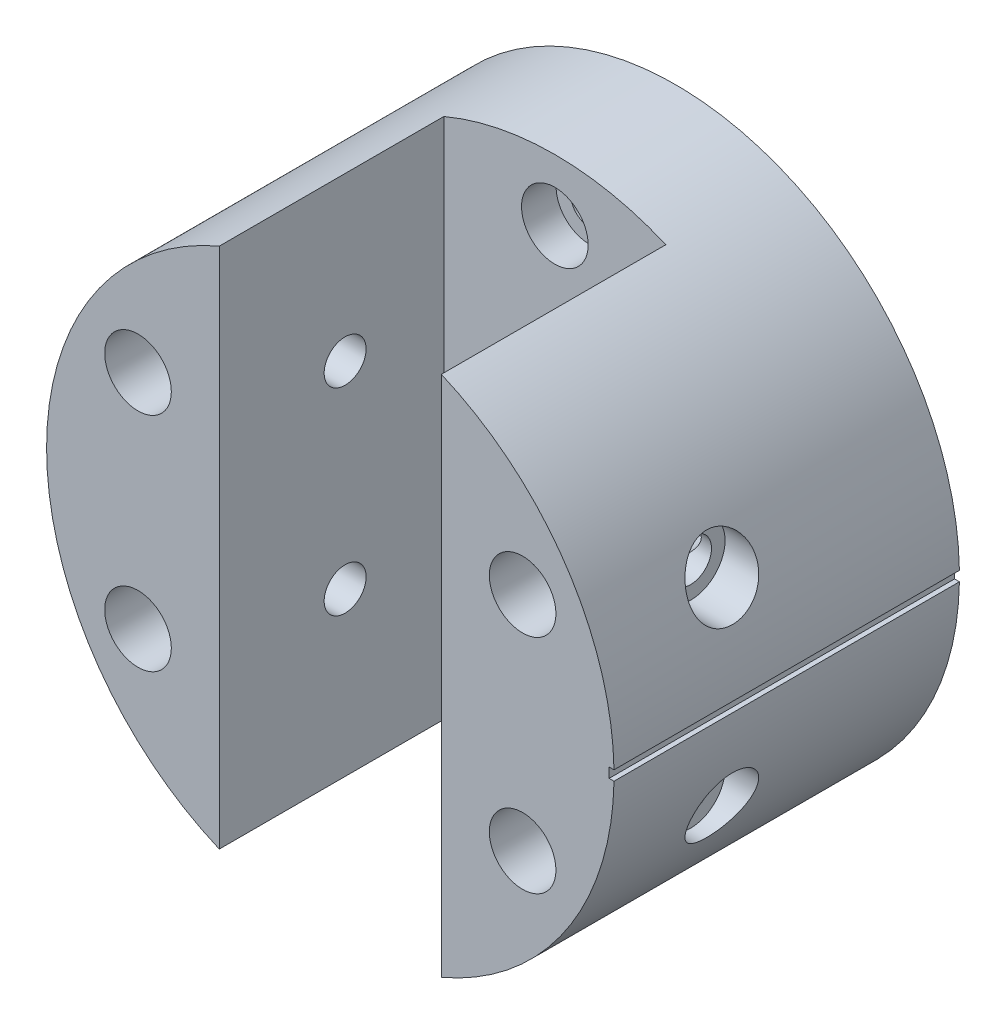
SolidWorks part; units mm, degrees
ref_plane "前视基准面" through (0, 0, 0) normal (0, 0, 1) x (1, 0, 0)
ref_plane "上视基准面" through (0, 0, 0) normal (0, 1, 0) x (1, 0, 0)
ref_plane "右视基准面" through (0, 0, 0) normal (1, 0, 0) x (0, 0, -1)
other "Configuration Table"
sketch "草图1" plane through (0, 0, 0) normal (0, 0, 1) x (1, 0, 0)
  circle A0 centre (0, 0) radius 23
extrude "凸台-拉伸1" add sketch "草图1" along normal blind 28
sketch "草图2" plane through (0, 0, 28) normal (0, 0, 1) x (1, 0, 0)
  line L0 (0, 0) -> (9, 0) construction
  line L1 (0, 0) -> (-9, 0) construction
  line L2 (-9, 21.166) -> (-9, -21.166)
  line L3 (9, 21.166) -> (9, -21.166)
  circle A0 centre (0, 0) radius 23 construction
  circle A1 centre (0, 0) radius 23
  circle M4 centre (0, 0) radius 23
extrude "切除-拉伸1" cut sketch "草图2" against normal blind 18.2 contours L3 L2 M4
sketch "草图3" plane through (0, 0, 28) normal (0, 0, 1) x (1, 0, 0)
  line L0 (0, 0) -> (0, 18) construction
  circle A0 centre (0, 18) radius 1.5
  circle A1 centre (15.5885, 9) radius 1.5
  circle A2 centre (15.5885, -9) radius 1.5
  circle A3 centre (0, -18) radius 1.5
  circle A4 centre (-15.5885, -9) radius 1.5
  circle A5 centre (-15.5885, 9) radius 1.5
  point P16 (0, 0)
  dimension "D1" = 6
extrude "切除-拉伸2" cut sketch "草图3" against normal through all
sketch "草图5" plane through (0, 0, 28) normal (0, 0, 1) x (1, 0, 0)
  circle A0 centre (0, 18) radius 2.7
  circle A1 centre (15.5885, 9) radius 2.7
  circle A2 centre (15.5885, -9) radius 2.7
  circle A3 centre (0, -18) radius 2.7
  circle A4 centre (-15.5885, -9) radius 2.7
  circle A5 centre (-15.5885, 9) radius 2.7
  point P15 (0, 0)
  dimension "D1" = 6
extrude "切除-拉伸3" cut sketch "草图5" against normal blind 21
sketch "草图7" plane through (9, 0, 0) normal (-1, 0, 0) x (0, 0, 1)
  line L0 (0, 0) -> (9.8, 0) construction
  line L1 (9.8, 0) -> (17.8, 0) construction
  line L2 (17.8, -8) -> (17.8, 8) construction
  circle A0 centre (17.8, 8) radius 1.7
  circle A1 centre (17.8, -8) radius 1.7
  point P7 (17.8, 0)
extrude "切除-拉伸4" cut sketch "草图7" against normal through all both and the other way through all
ref_plane "基准面1" through (23, 0, 0) normal (-1, 0, 0) x (0, 0, 1)
sketch "草图8" plane through (23, 0, 0) normal (-1, 0, 0) x (0, 0, 1)
  circle A0 centre (17.8, 8) radius 2.8
  circle A1 centre (17.8, -8) radius 2.8
extrude "切除-拉伸5" cut sketch "草图8" along normal blind 4
sketch "草图9" plane through (23, 0, 0) normal (-1, 0, 0) x (0, 0, 1)
  line L1 (-31.1599, 0.4) -> (31.1599, 0.4)
  line L2 (-31.1599, 0.4) -> (-31.1599, -0.4)
  line L3 (-31.1599, -0.4) -> (31.1599, -0.4)
  line L4 (31.1599, 0.4) -> (31.1599, -0.4)
  line L5 (-31.1599, 0.4) -> (31.1599, -0.4) construction
  line L6 (-31.1599, -0.4) -> (31.1599, 0.4) construction
  point P0 (0, 0)
extrude "切除-拉伸6" cut sketch "草图9" along normal blind 0.4
